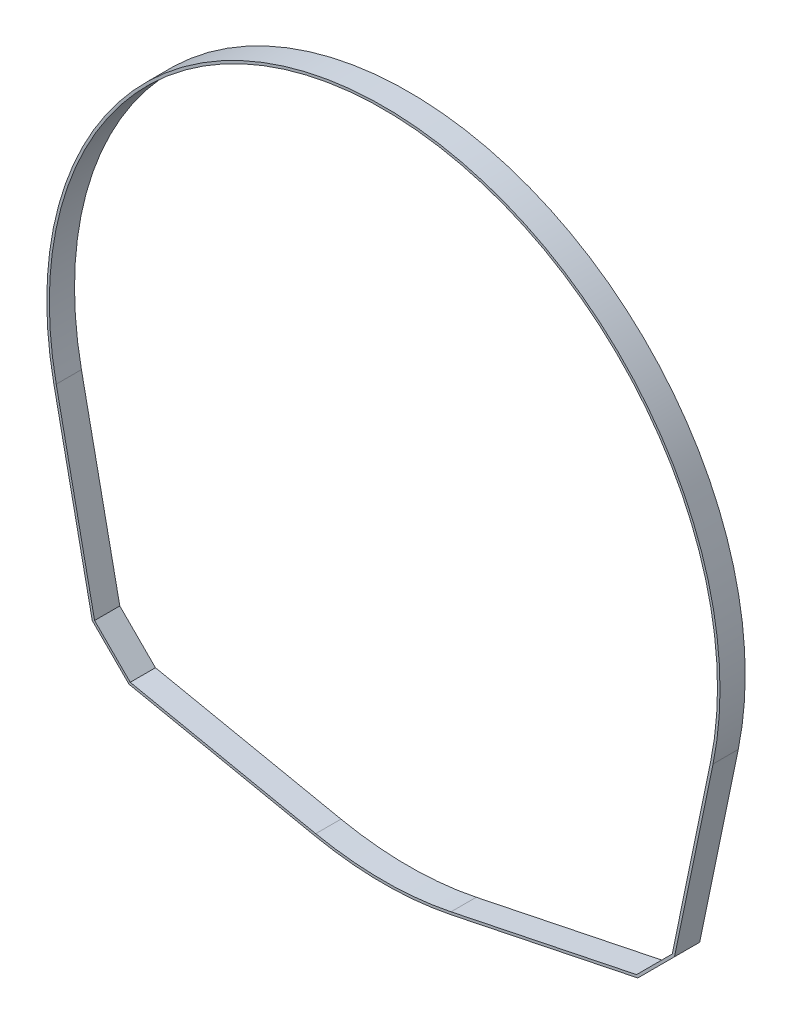
SolidWorks part; units mm, degrees
material "Plain Carbon Steel"
ref_plane "Front Plane" through (0, 0, 0) normal (0, 0, 1) x (1, 0, 0)
ref_plane "Top Plane" through (0, 0, 0) normal (0, 1, 0) x (1, 0, 0)
ref_plane "Right Plane" through (0, 0, 0) normal (1, 0, 0) x (0, 0, -1)
sketch "Sketch1" plane through (0, 0, 0) normal (0, 0, 1) x (1, 0, 0)
  line L0 (-72.7347, -47.3347) -> (-72.7347, -72.7347) construction
  line L1 (-72.7347, -72.7347) -> (-47.3347, -72.7347) construction
  line L2 (47.3347, -72.7347) -> (72.7347, -72.7347) construction
  line L3 (72.7347, -72.7347) -> (72.7347, -47.3347) construction
  line L4 (63.7544, -72.7347) -> (72.7347, -63.7544)
  line L5 (-72.7347, -63.7544) -> (-63.7544, -72.7347)
  line L6 (-72.7347, -63.7544) -> (-82.3946, -17.0369)
  line L7 (-63.7544, -72.7347) -> (-17.0369, -82.3946)
  line L8 (63.7544, -72.7347) -> (17.0369, -82.3946)
  line L9 (72.7347, -63.7544) -> (82.3946, -17.0369)
  line L10 (-73.318, -64.0691) -> (-83.0164, -17.1655)
  line L11 (73.318, -64.0691) -> (83.0164, -17.1655)
  line L12 (64.0691, -73.318) -> (73.318, -64.0691)
  line L13 (64.0691, -73.318) -> (17.1655, -83.0164)
  line L14 (-64.0691, -73.318) -> (-17.1655, -83.0164)
  line L15 (-73.318, -64.0691) -> (-64.0691, -73.318)
  line L16 (-72.7347, -47.3347) -> (-69.5597, -47.3347) construction
  line L17 (-47.3347, -72.7347) -> (-47.3347, -69.5597) construction
  line L18 (47.3347, -72.7347) -> (47.3347, -69.5597) construction
  line L19 (72.7347, -47.3347) -> (69.5597, -47.3347) construction
  arc A0 (-82.3946, -17.0369) -> (82.3946, -17.0369) centre (0, 0) cw
  circle A1 centre (0, 0) radius 84.1375 construction
  arc A2 (-17.0369, -82.3946) -> (17.0369, -82.3946) centre (0, 0) ccw
  arc A3 (-83.0164, -17.1655) -> (83.0164, -17.1655) centre (0, 0) cw
  arc A4 (-17.1655, -83.0164) -> (17.1655, -83.0164) centre (0, 0) ccw
  dimension "D1" = 168.275
  dimension "D2" = 25.4
  dimension "D3" = 25.4
  dimension "D4" = 45
  dimension "D5" = 6.35
  dimension "D6" = 45
  dimension "D8" = 3.175
  dimension "D7" = 0.635
extrude "Boss-Extrude1" add sketch "Sketch1" along normal blind 6.35
